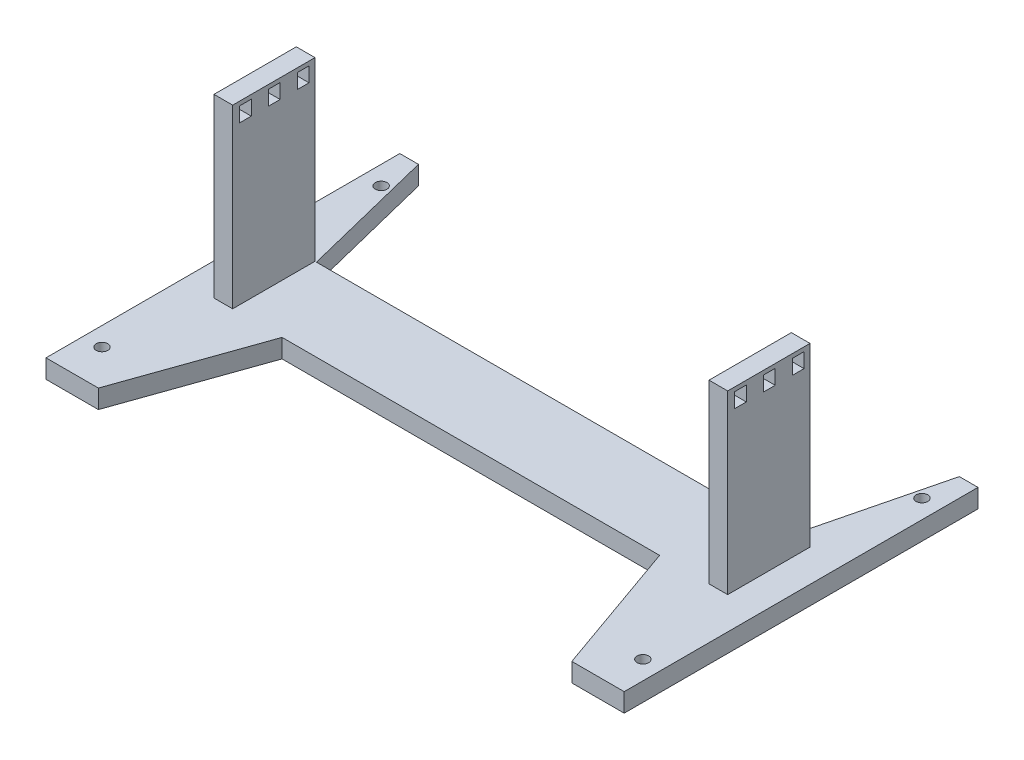
SolidWorks part; units mm, degrees
ref_plane "Front" through (0, 0, 0) normal (0, 0, 1) x (1, 0, 0)
ref_plane "Top" through (0, 0, 0) normal (0, 1, 0) x (1, 0, 0)
ref_plane "Right" through (0, 0, 0) normal (1, 0, 0) x (0, 0, -1)
sketch "草图1" plane through (0, 0, 0) normal (0, 1, 0) x (1, 0, 0)
  line L0 (98.0231, -74.9268) -> (98.0231, 75.0732) construction
  line L1 (98.0231, 75.0732) -> (-0.2933, 75.0732) construction
  line L2 (-0.2933, 75.0732) -> (-0.2933, -74.9268) construction
  line L3 (91.6731, -74.9268) -> (91.6731, -62.2268) construction
  line L4 (80.2067, -74.9268) -> (80.2067, -0.7668) construction
  line L5 (-0.2933, -74.9268) -> (80.2067, -74.9268) construction
  line L6 (80.2067, -0.7668) -> (63.9043, -0.7668) construction
  line L7 (63.9043, -0.7668) -> (63.9043, -28.7668) construction
  line L8 (63.9043, -28.7668) -> (80.2067, -28.7668) construction
  line L9 (63.9043, -14.7668) -> (-0.2933, -14.7668) construction
  line L10 (91.6731, 45.3932) -> (91.6731, 32.6932) construction
  line L11 (98.0231, -74.9268) -> (91.6731, -74.9268)
  line L12 (91.6731, -74.9268) -> (80.2067, -74.9268)
  line L13 (80.2067, -74.9268) -> (63.9043, -28.7668)
  line L14 (63.9043, -28.7668) -> (-64.491, -28.7668)
  line L15 (63.9043, -0.7668) -> (80.2067, -0.7668)
  line L16 (80.2067, -0.7668) -> (91.6731, 45.3932)
  line L17 (91.6731, 45.3932) -> (98.0231, 45.3932)
  line L18 (98.0231, 45.3932) -> (98.0231, -74.9268)
  line L19 (63.9043, -0.7668) -> (-64.491, -0.7668)
  line L20 (-64.491, -0.7668) -> (-80.7933, -0.7668)
  line L21 (-80.7933, -0.7668) -> (-92.2597, 45.3932)
  line L22 (-92.2597, 45.3932) -> (-98.6097, 45.3932)
  line L23 (-98.6097, 45.3932) -> (-98.6097, -74.9268)
  line L24 (-98.6097, -74.9268) -> (-92.2597, -74.9268)
  line L25 (-92.2597, -74.9268) -> (-80.7933, -74.9268)
  line L26 (-80.7933, -74.9268) -> (-64.491, -28.7668)
  circle A0 centre (91.6731, -62.2268) radius 1.984
  circle A1 centre (91.6731, 32.6932) radius 1.984
  circle A2 centre (-92.2597, -62.2268) radius 1.984
  circle A3 centre (-92.2597, 32.6932) radius 1.984
  point P3 (0, 0)
  point P25 (-0.2933, -0.7668)
  point P32 (-0.2933, -28.7668)
extrude "凸台-拉伸1" add sketch "草图1" along normal blind 6.35
sketch "草图2" plane through (0, 6.35, 0) normal (0, 1, 0) x (1, 0, 0)
  line L0 (-80.7933, -0.7668) -> (-81.2933, -0.7668) construction
  line L1 (-81.2933, -0.7668) -> (-81.2933, -28.7668) construction
  line L2 (-81.2933, -28.7668) -> (-87.6433, -28.7668) construction
  line L3 (-87.6433, -28.7668) -> (-87.6433, -0.7668) construction
  line L4 (-87.6433, -0.7668) -> (-81.2933, -0.7668) construction
  line L5 (-0.2933, -28.7668) -> (-0.2933, 14.2296) construction
  line L6 (-64.491, -28.7668) -> (63.9043, -28.7668) construction
  line L7 (-87.6433, -0.7668) -> (-81.2933, -0.7668)
  line L8 (-81.2933, -0.7668) -> (-81.2933, -28.7668)
  line L9 (-81.2933, -28.7668) -> (-87.6433, -28.7668)
  line L10 (-87.6433, -28.7668) -> (-87.6433, -0.7668)
  line L11 (80.7067, -28.7668) -> (87.0567, -28.7668)
  line L12 (80.7067, -0.7668) -> (80.7067, -28.7668)
  line L13 (87.0567, -0.7668) -> (80.7067, -0.7668)
  line L14 (87.0567, -28.7668) -> (87.0567, -0.7668)
extrude "凸台-拉伸2" add sketch "草图2" along normal blind 60
sketch "草图3" plane through (87.0567, 0, 0) normal (1, 0, 0) x (0, 0, -1)
  line L0 (-0.7668, 66.35) -> (-4.7968, 66.35) construction
  line L1 (-28.7668, 66.35) -> (-0.7668, 66.35) construction
  line L2 (-4.7968, 66.35) -> (-4.7968, 62.44) construction
  line L3 (-4.7968, 62.44) -> (-14.6168, 62.44) construction
  line L4 (-14.6168, 62.44) -> (-14.6168, 66.35) construction
  line L5 (-14.6168, 66.35) -> (-24.4368, 66.35) construction
  line L6 (-24.4368, 66.35) -> (-24.4368, 62.44) construction
  line L7 (-22.4368, 62.44) -> (-22.4368, 59.94)
  line L8 (-22.4368, 59.94) -> (-26.4368, 59.94)
  line L9 (-26.4368, 59.94) -> (-26.4368, 64.94)
  line L10 (-26.4368, 64.94) -> (-22.4368, 64.94)
  line L11 (-22.4368, 64.94) -> (-22.4368, 62.44)
  line L12 (-16.6168, 62.44) -> (-16.6168, 59.94)
  line L13 (-16.6168, 59.94) -> (-12.6168, 59.94)
  line L14 (-12.6168, 59.94) -> (-12.6168, 64.94)
  line L15 (-12.6168, 64.94) -> (-16.6168, 64.94)
  line L16 (-16.6168, 64.94) -> (-16.6168, 62.44)
  line L17 (-6.7968, 62.44) -> (-6.7968, 64.94)
  line L18 (-6.7968, 64.94) -> (-2.7968, 64.94)
  line L19 (-2.7968, 64.94) -> (-2.7968, 59.94)
  line L20 (-2.7968, 59.94) -> (-6.7968, 59.94)
  line L21 (-6.7968, 62.44) -> (-6.7968, 59.94)
extrude "切除-拉伸1" cut sketch "草图3" against normal blind 250
